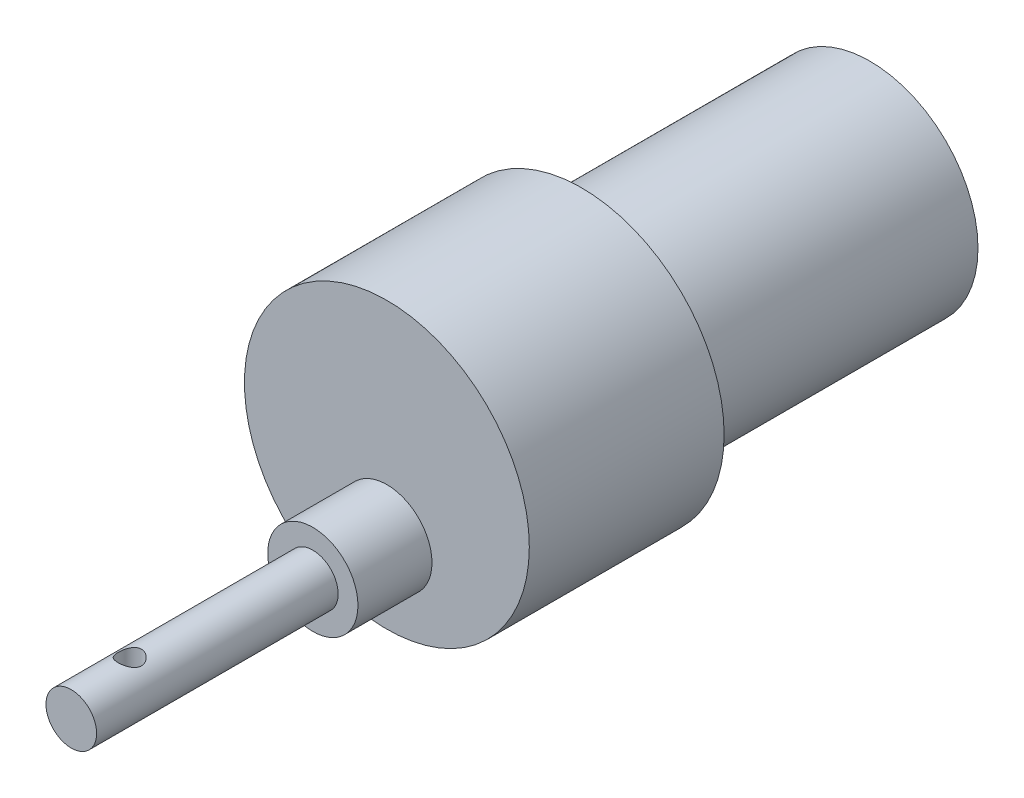
SolidWorks part; units mm, degrees
material "Copper"
ref_plane "Front Plane" through (0, 0, 0) normal (0, 0, 1) x (1, 0, 0)
ref_plane "Top Plane" through (0, 0, 0) normal (0, 1, 0) x (1, 0, 0)
ref_plane "Right Plane" through (0, 0, 0) normal (1, 0, 0) x (0, 0, -1)
ref_plane "Plane1" through (0, 0, 37) normal (0, 0, 1) x (1, 0, 0)
sketch "Sketch6" plane through (0, 0, 0) normal (0, 0, 1) x (1, 0, 0)
  circle A0 centre (0, 0) radius 13.86
  dimension "D1" = 27.72
extrude "Boss-Extrude4" add sketch "Sketch6" along normal blind 62
sketch "Sketch7" plane through (0, 0, 37) normal (0, 0, 1) x (1, 0, 0)
  circle A0 centre (0, 0) radius 18.28
  dimension "D1" = 36.56
extrude "Boss-Extrude5" add sketch "Sketch7" along normal blind 25
sketch "Sketch8" plane through (0, 0, 62) normal (0, 0, 1) x (1, 0, 0)
  circle A0 centre (0, -7.99) radius 5.79
  dimension "D2" = 11.58
  dimension "D1" = 7.99
extrude "Boss-Extrude6" add sketch "Sketch8" along normal blind 9.5
sketch "Sketch9" plane through (0, 0, 71.5) normal (0, 0, 1) x (1, 0, 0)
  circle A0 centre (0, -7.99) radius 3.25
  dimension "D1" = 6.5
extrude "Boss-Extrude7" add sketch "Sketch9" along normal blind 31
ref_plane "Plane2" through (0, 18.28, 0) normal (0, 1, 0) x (1, 0, 0)
ref_plane "Plane3" through (0, 0, 97) normal (0, 0, 1) x (1, 0, 0)
sketch "Sketch11" plane through (0, 0, 97) normal (0, 0, 1) x (1, 0, 0)
  circle A0 centre (0, -7.99) radius 3.25
  dimension "D1" = 6.5
sketch "Sketch13" plane through (0, 0, 0) normal (0, 1, 0) x (1, 0, 0)
  circle A0 centre (0, -95) radius 1.5
  dimension "D1" = 3
  dimension "D2" = 95
extrude "Cut-Extrude1" cut sketch "Sketch13" against normal blind 20
